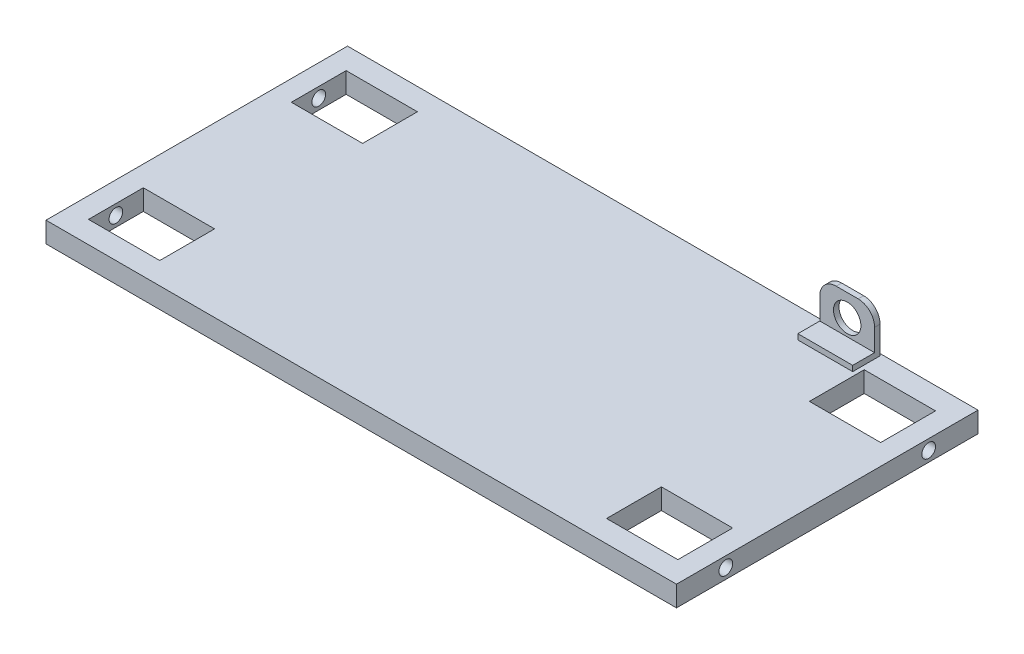
SolidWorks part; units mm, degrees
material "ABS PC"
ref_plane "前视基准面" through (0, 0, 0) normal (0, 0, 1) x (1, 0, 0)
ref_plane "上视基准面" through (0, 0, 0) normal (0, 1, 0) x (1, 0, 0)
ref_plane "右视基准面" through (0, 0, 0) normal (1, 0, 0) x (0, 0, -1)
sketch "Sketch1" plane through (0, 0, 0) normal (0, 1, 0) x (1, 0, 0)
  line L1 (146.05, -69.85) -> (-146.05, -69.85)
  line L2 (146.05, -69.85) -> (146.05, 69.85)
  line L3 (146.05, 69.85) -> (-146.05, 69.85)
  line L4 (-146.05, -69.85) -> (-146.05, 69.85)
  line L5 (146.05, -69.85) -> (-146.05, 69.85) construction
  line L6 (146.05, 69.85) -> (-146.05, -69.85) construction
  point P1 (0, 0)
  dimension "D1" = 139.7
  dimension "D2" = 292.1
extrude "Boss-Extrude1" add sketch "Sketch1" along normal blind 9.525
sketch "Sketch2" plane through (0, 9.525, 0) normal (0, 1, 0) x (1, 0, 0)
  line L0 (-146.05, 0) -> (146.05, 0) construction
  line L1 (-146.05, 69.85) -> (-146.05, -69.85) construction
  line L2 (146.05, -69.85) -> (146.05, 69.85) construction
  line L3 (0, 69.85) -> (0, -69.85) construction
  line L4 (146.05, 69.85) -> (-146.05, 69.85) construction
  line L5 (-146.05, -69.85) -> (146.05, -69.85) construction
  line L6 (-136.525, 34.29) -> (-103.505, 34.29)
  line L7 (-103.505, -59.69) -> (-136.525, -59.69)
  line L8 (-103.505, -59.69) -> (-103.505, -34.29)
  line L9 (-103.505, 59.69) -> (-136.525, 59.69)
  line L10 (-136.525, -59.69) -> (-136.525, -34.29)
  line L11 (-103.505, -59.69) -> (-136.525, 59.69) construction
  line L12 (-103.505, 59.69) -> (-136.525, -59.69) construction
  line L13 (-136.525, -34.29) -> (-103.505, -34.29)
  line L14 (-103.505, 34.29) -> (-103.505, 59.69)
  line L15 (-136.525, 34.29) -> (-136.525, 59.69)
  line L16 (103.505, 34.29) -> (103.505, 59.69)
  line L17 (136.525, 34.29) -> (103.505, 34.29)
  line L18 (136.525, 34.29) -> (136.525, 59.69)
  line L19 (103.505, 59.69) -> (136.525, 59.69)
  line L20 (103.505, -59.69) -> (136.525, -59.69)
  line L21 (103.505, -59.69) -> (103.505, -34.29)
  line L22 (136.525, -59.69) -> (136.525, -34.29)
  line L23 (136.525, -34.29) -> (103.505, -34.29)
  point P12 (-120.015, 0)
  dimension "D1" = 10.16
  dimension "D2" = 33.02
  dimension "D3" = 25.4
  dimension "D4" = 9.525
extrude "Cut-Extrude1" cut sketch "Sketch2" against normal up to surface (9.525 mm away) up to face at (0, 0, 0)
sketch "Sketch3" plane through (146.05, 0, 0) normal (1, 0, 0) x (0, 0, -1)
  line L0 (-69.85, 4.7625) -> (69.85, 4.7625) construction
  line L1 (-69.85, 9.525) -> (-69.85, 0) construction
  line L2 (69.85, 9.525) -> (69.85, 0) construction
  line L3 (0, 9.525) -> (0, 0) construction
  line L4 (-69.85, 9.525) -> (69.85, 9.525) construction
  circle A0 centre (-46.99, 4.7625) radius 3.175
  circle A1 centre (46.99, 4.7625) radius 3.175
  point P15 (0, 0)
  point P16 (0, 0)
  point P17 (0, 0)
  dimension "D1" = 6.35
  dimension "D2" = 22.86
extrude "Cut-Extrude2" cut sketch "Sketch3" against normal blind 9.525
ref_plane "Plane1" through (0, 0, 0) normal (1, 0, 0) x (0, 0, -1)
mirror "Mirror1" about plane through (0, 0, 0) normal (1, 0, 0) of "Cut-Extrude2"
sketch "Sketch4" plane through (0, 9.525, 0) normal (0, 1, 0) x (1, 0, 0)
  line L0 (146.05, -69.85) -> (146.05, 69.85) construction
  line L1 (76.2, 68.9407) -> (101.6, 68.9407)
  line L2 (76.2, 68.9407) -> (76.2, 56.2407)
  line L3 (76.2, 56.2407) -> (101.6, 56.2407)
  line L4 (101.6, 68.9407) -> (101.6, 56.2407)
  line L5 (146.05, 69.85) -> (-146.05, 69.85) construction
  point P4 (88.9, 68.9407)
  dimension "D1" = 25.4
  dimension "D2" = 57.15
  dimension "D3" = 12.7
  dimension "D4" = 0.9093
extrude "Boss-Extrude2" add sketch "Sketch4" along normal blind 20.32
sketch "Sketch5" plane through (0, 29.845, 0) normal (0, 1, 0) x (1, 0, 0)
  line L0 (76.2, 68.9407) -> (76.2, 56.2407) construction
  line L1 (76.2, 66.4007) -> (101.6, 66.4007)
  line L2 (76.2, 66.4007) -> (76.2, 56.2407)
  line L3 (76.2, 56.2407) -> (101.6, 56.2407)
  line L4 (101.6, 66.4007) -> (101.6, 56.2407)
  line L5 (101.6, 68.9407) -> (76.2, 68.9407) construction
  dimension "D1" = 2.54
extrude "Cut-Extrude3" cut sketch "Sketch5" against normal blind 17.78
sketch "Sketch6" plane through (0, 0, -68.9407) normal (0, 0, -1) x (-1, 0, 0)
  line L0 (-101.6, 29.845) -> (-76.2, 9.525) construction
  circle A0 centre (-88.9, 19.685) radius 6.35
  point P4 (-88.9, 19.685)
  dimension "D1" = 12.7
fillet "Fillet2" radius 7.62 2 edges at (76.2, 29.845, -67.6707) (101.6, 29.845, -67.6707)
extrude "Cut-Extrude4" cut sketch "Sketch6" against normal up to surface (2.54 mm away) contours A0 up to face at (88.9, 21.9044, -66.4007)
